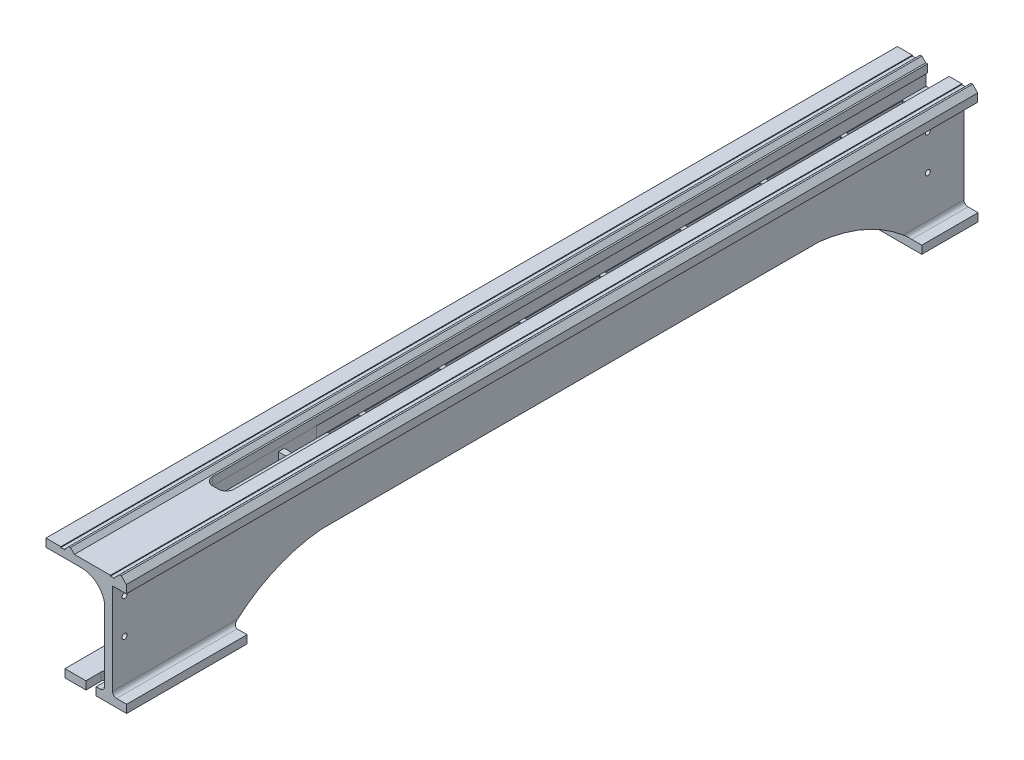
SolidWorks part; units mm, degrees
ref_plane "Front Plane" through (0, 0, 0) normal (0, 0, 1) x (1, 0, 0)
ref_plane "Top Plane" through (0, 0, 0) normal (0, 1, 0) x (1, 0, 0)
ref_plane "Right Plane" through (0, 0, 0) normal (1, 0, 0) x (0, 0, -1)
sketch "Sketch1" plane through (0, 0, 0) normal (0, 0, 1) x (1, 0, 0)
  line L0 (-31.5551, 31.2902) -> (-37.8538, 37.7187)
  line L2 (-131.555, 31.42) -> (-131.555, 21.42)
  line L4 (-31.5551, 31.2902) -> (-31.5551, 21.2902)
  line L5 (-37.8538, 37.7187) -> (-39.8538, 37.7187)
  line L6 (-39.8538, 37.7187) -> (-46.2824, 31.42)
  line L7 (-46.2824, 31.42) -> (-46.2824, 30.42)
  line L8 (-46.2824, 30.42) -> (-51.2824, 30.42)
  line L9 (-51.2824, 30.42) -> (-51.2824, 31.42)
  line L10 (-51.2824, 31.42) -> (-96.2063, 31.42)
  line L14 (-96.2063, 31.42) -> (-101.1053, 36.42)
  line L15 (-101.1053, 36.42) -> (-103.1053, 36.42)
  line L16 (-103.1053, 36.42) -> (-108.055, 31.4703)
  line L17 (-108.055, 31.4703) -> (-108.055, 30.42)
  line L18 (-108.055, 30.42) -> (-113.055, 30.42)
  line L19 (-113.055, 30.42) -> (-113.055, 31.42)
  line L20 (-113.055, 31.42) -> (-131.555, 31.42)
  line L21 (-131.555, 21.42) -> (-87.3496, 21.42)
  line L22 (-31.5551, 21.2902) -> (-48.7011, 21.2902)
  line L23 (-48.7011, 21.2902) -> (-48.7011, -92.58)
  line L24 (-43.7011, -97.58) -> (-31.1954, -97.58)
  line L25 (-31.1954, -97.58) -> (-31.1954, -107.58)
  line L26 (-31.1954, -107.58) -> (-108.01, -107.58)
  line L27 (-108.01, -107.58) -> (-108.01, -97.58)
  line L28 (-108.01, -97.58) -> (-63.7011, -97.58)
  line L29 (-58.7011, -92.58) -> (-58.7011, -1.9527)
  arc A0 (-87.3496, 21.42) -> (-58.7011, -1.9527) centre (-87.3496, -7.8239) cw
  arc A1 (-48.7011, -92.58) -> (-43.7011, -97.58) centre (-43.7011, -92.58) ccw
  arc A2 (-63.7011, -97.58) -> (-58.7011, -92.58) centre (-63.7011, -92.58) ccw
  point P30 (-48.7011, -97.58)
  dimension "D17" = 5
  dimension "D1" = 100
  dimension "D2" = 7
  dimension "D3" = 2
  dimension "D4" = 5
  dimension "D5" = 18.5
  dimension "D6" = 5
  dimension "D7" = 10
  dimension "D8" = 135
  dimension "D9" = 9
  dimension "D10" = 9
  dimension "D11" = 2
  dimension "D12" = 7
  dimension "D13" = 10
  dimension "D14" = 5
  dimension "D15" = 10
  dimension "D16" = 139
  dimension "D18" = 10
  dimension "D19" = 1
extrude "Boss-Extrude1" add sketch "Sketch1" along normal blind 1060
sketch "Sketch2" plane through (0, 20.7647, 0) normal (0, 1, 0) x (1, 0, 0)
  line L0 (-94.1707, -1200) -> (-94.1707, 0) construction
  line L1 (-84.1707, 100) -> (-77.1707, 100)
  line L2 (-94.1707, 90) -> (-94.1707, -890)
  line L3 (-84.1707, -900) -> (-77.1707, -900)
  line L4 (-67.1707, 90) -> (-67.1707, -890)
  line L5 (-67.1707, -1200) -> (-67.1707, 0) construction
  line L6 (-51.2824, 0) -> (-96.2063, 0) construction
  arc A0 (-94.1707, -890) -> (-84.1707, -900) centre (-84.1707, -890) ccw
  arc A1 (-77.1707, -900) -> (-67.1707, -890) centre (-77.1707, -890) ccw
  arc A2 (-77.1707, 100) -> (-67.1707, 90) centre (-77.1707, 90) cw
  arc A3 (-84.1707, 100) -> (-94.1707, 90) centre (-84.1707, 90) ccw
  point P12 (-67.1707, -900)
  point P15 (-67.1707, 100)
  point P18 (-94.1707, 100)
  dimension "D2" = 10
  dimension "D1" = 1000
  dimension "D3" = 100
extrude "Cut-Extrude1" cut sketch "Sketch2" along normal blind 800
sketch "Sketch5" plane through (0, 0, 0) normal (0, 0, -1) x (-1, 0, 0)
  line L1 (105.3464, -97.4955) -> (94.9198, -97.4955)
  line L2 (105.3464, -97.4955) -> (105.3464, 27.7967)
  line L3 (105.3464, 27.7967) -> (94.9198, 27.7967)
  line L4 (94.9198, -97.4955) -> (94.9198, 27.7967)
extrude "Boss-Extrude2" add sketch "Sketch5" against normal blind 950
sketch "Sketch6" plane through (-105.3464, 0, 0) normal (-1, 0, 0) x (0, 0, 1)
  line L0 (0, -97.4955) -> (0, 21.42) construction
  line L1 (0, 16.5847) -> (7.4351, 16.5847)
  line L2 (0, 16.5847) -> (0, -47.4448)
  line L3 (0, -47.4448) -> (7.4351, -47.4448)
  line L4 (7.4351, 16.5847) -> (7.4351, -47.4448)
extrude "Boss-Extrude3" add sketch "Sketch6" against normal blind 50
pattern_linear "LPattern1" count 10 spacing 100 along (0, 0, 1) of "Boss-Extrude3"
sketch "Sketch4" plane through (-31.5551, 0, 0) normal (1, 0, 0) x (0, 0, -1)
  line L0 (-910, -97.58) -> (-910, -107.58)
  line L1 (-1060, -97.58) -> (0, -97.58) construction
  line L2 (-1060, -107.58) -> (0, -107.58) construction
  line L3 (-910, -107.58) -> (-910, -177.9566)
  line L4 (-910, -177.9566) -> (-70, -177.9566)
  line L5 (-70, -177.9566) -> (-70, -97.58)
  line L6 (-800, -47.58) -> (-180.0688, -47.58)
  line L7 (0, -92.58) -> (0, 21.2902) construction
  line L8 (-1060, -92.58) -> (-1060, 21.2902) construction
  arc A1 (-800, -47.58) -> (-910, -97.58) centre (-783.4011, -230.0975) ccw
  arc A2 (-180.0688, -47.58) -> (-70, -97.58) centre (-201.6096, -241.1508) cw
  dimension "D1" = 60
  dimension "D2" = 70
  dimension "D3" = 150
  dimension "D4" = 110
  dimension "D5" = 110.0688
extrude "Cut-Extrude3" cut sketch "Sketch4" against normal blind 100 and the other way blind 10
sketch "Sketch3" plane through (0, 0, 1060) normal (0, 0, 1) x (1, 0, 0)
  line L0 (-51.2824, 31.42) -> (-96.2063, 31.42) construction
  line L1 (-58.7011, 6.42) -> (-95.7995, 6.42)
  line L2 (-58.7011, 6.42) -> (-58.7011, 21.42)
  line L3 (-58.7011, 21.42) -> (-95.7995, 21.42)
  line L4 (-95.7995, 6.42) -> (-95.7995, 21.42)
  line L5 (-58.7011, -1.9527) -> (-58.7011, -47.4448) construction
  dimension "D1" = 15
  dimension "D2" = 10
extrude "Cut-Extrude2" cut sketch "Sketch3" against normal blind 1000 from offset 300 offset against normal yes
sketch "Sketch7" plane through (0, 0, 0) normal (0, 0, -1) x (-1, 0, 0)
  line L0 (58.7011, 6.42) -> (95.7995, 6.42) construction
  line L1 (99.7499, 6.42) -> (57.7636, 6.42)
  line L2 (99.7499, 6.42) -> (99.7499, -7.7909)
  line L3 (99.7499, -7.7909) -> (57.7636, -7.7909)
  line L4 (57.7636, 6.42) -> (57.7636, -7.7909)
extrude "Boss-Extrude4" add sketch "Sketch7" against normal blind 30
sketch "Sketch8" plane through (0, 6.42, 0) normal (0, 1, 0) x (1, 0, 0)
  circle A0 centre (-79.7891, -14.9723) radius 3.8743
extrude "Cut-Extrude4" cut sketch "Sketch8" against normal blind 30
sketch "Эскиз1" plane through (-48.7011, 0, 0) normal (1, 0, 0) x (0, 0, -1)
  line L0 (0, -92.58) -> (0, 21.2902) construction
  line L1 (-1060, 21.2902) -> (0, 21.2902) construction
  circle A0 centre (-45, 3.2902) radius 3.1675
  dimension "D1" = 45
  dimension "D2" = 18
extrude "Вырез-Вытянуть1" cut sketch "Эскиз1" against normal blind 10
pattern_linear "Линейный массив1" count 2 spacing 44 along (0, -1, 0) count 2 spacing 1000 along (0, 0, 1) of "Вырез-Вытянуть1"
sketch "Sketch9" plane through (0, -107.58, 0) normal (0, -1, 0) x (1, 0, 0)
  circle A0 centre (-75.4322, 36.0661) radius 6.088
extrude "Cut-Extrude5" cut sketch "Sketch9" against normal blind 10
pattern_linear "LPattern2" count 2 spacing 1005 along (0, 0, 1) of "Cut-Extrude5"
sketch "Sketch10" plane through (0, -107.58, 0) normal (0, -1, 0) x (1, 0, 0)
  line L0 (-75.4322, 1041.0661) -> (-75.4322, 1067.2294) construction
  line L1 (-81.8186, 1041.0661) -> (-81.8186, 1067.2294)
  line L2 (-69.0457, 1041.0661) -> (-69.0457, 1067.2294)
  arc A0 (-81.8186, 1041.0661) -> (-69.0457, 1041.0661) centre (-75.4322, 1041.0661) ccw
  arc A1 (-69.0457, 1067.2294) -> (-81.8186, 1067.2294) centre (-75.4322, 1067.2294) ccw
  point P3 (-75.4322, 1054.1478)
extrude "Cut-Extrude6" cut sketch "Sketch10" against normal blind 10
